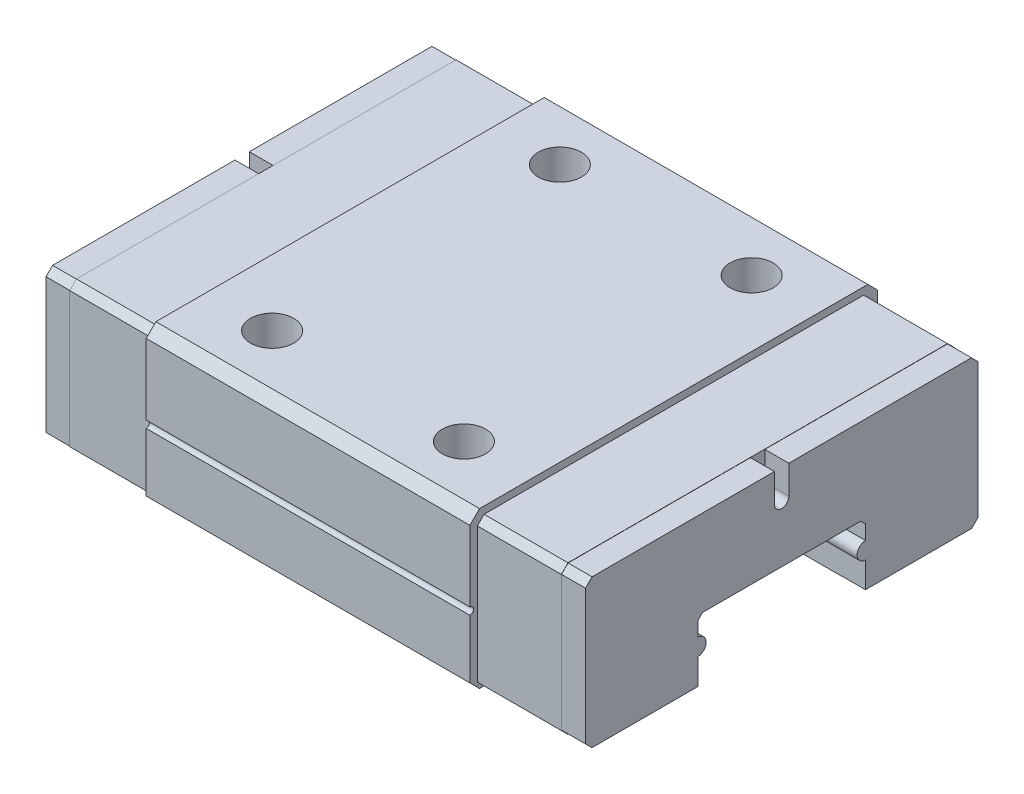
SolidWorks part; units mm, degrees
material "铸造合金钢"
ref_plane "前视基准面" through (0, 0, 0) normal (0, 0, 1) x (1, 0, 0)
ref_plane "上视基准面" through (0, 0, 0) normal (0, 1, 0) x (1, 0, 0)
ref_plane "右视基准面" through (0, 0, 0) normal (1, 0, 0) x (0, 0, -1)
sketch "草图1" plane through (0, 0, 0) normal (1, 0, 0) x (0, 0, -1)
  line L0 (0, 0) -> (0, 6.9969) construction
  line L1 (0, 0) -> (6.5228, 0) construction
  line L2 (-8.5, 2.8469) -> (-8.0969, 3.25)
  line L3 (-8.0969, 3.25) -> (8.0969, 3.25)
  line L4 (-8.5, 2.8469) -> (-8.5, -2.8469)
  line L5 (-8.0969, -3.25) -> (8.0969, -3.25)
  line L6 (8.5, 2.8469) -> (8.5, -2.8469)
  line L7 (-8.5, 3.25) -> (8.5, -3.25) construction
  line L8 (-8.5, -3.25) -> (8.5, 3.25) construction
  line L9 (8.0969, 3.25) -> (8.5, 2.8469)
  line L10 (8.0969, -3.25) -> (8.5, -2.8469)
  line L11 (-8.5, -2.8469) -> (-8.0969, -3.25)
  point P1 (0, 0)
  dimension "D1" = 6.5
  dimension "D2" = 17
  dimension "D3" = 0.57
  dimension "D5" = 0.57
  dimension "D9" = 0.57
  dimension "D10" = 225
  dimension "D7" = 0.57
  dimension "D4" = 225
  dimension "D6" = 225
  dimension "D8" = 225
extrude "凸台-拉伸1" add sketch "草图1" along normal blind 13.5
sketch "草图3" plane through (0, 0, 0) normal (-1, 0, 0) x (0, 0, 1)
  line L0 (0, 0) -> (0, 6.7455) construction
  line L1 (0, 0) -> (9.8711, 0) construction
  line L3 (8.5, 2.8469) -> (8.5, -2.8469) construction
  circle A0 centre (8.5, -0.2531) radius 0.15
  circle A1 centre (-8.5, -0.2531) radius 0.15
  dimension "D1" = 0.3
  dimension "D2" = 3.1
extrude "切除-拉伸2" cut sketch "草图3" against normal up to surface (13.5 mm away) up to face at (13.5, 0, 0)
sketch "草图4" plane through (0, 0, 0) normal (-1, 0, 0) x (0, 0, 1)
  line L0 (0, 0) -> (0, 6.8579) construction
  line L1 (0, 0) -> (4.1985, 0) construction
  line L3 (8.19, -2.9702) -> (8.19, 2.67)
  line L4 (-8.2, -2.9702) -> (-8.2, 2.67)
  line L5 (7.91, 2.95) -> (-7.92, 2.95)
  line L6 (8.0969, -3.25) -> (-8.0969, -3.25) construction
  line L7 (-8.2, 2.95) -> (8.2, -3.25) construction
  line L8 (8.19, 2.95) -> (-8.21, -3.25) construction
  line L9 (-8.0969, 3.25) -> (8.0969, 3.25) construction
  line L10 (-8.5, -2.8469) -> (-8.5, -0.4031) construction
  line L11 (-8.2, 2.67) -> (-7.92, 2.95)
  line L12 (-7.9302, -3.24) -> (-8.2, -2.9702)
  line L13 (7.9202, -3.24) -> (8.19, -2.9702)
  line L14 (8.19, 2.67) -> (7.91, 2.95)
  line L15 (-7.9302, -3.24) -> (7.9202, -3.24)
  point P12 (0, -0.15)
  dimension "D1" = 0.3
  dimension "D2" = 0.3
  dimension "D3" = 0.01
  dimension "D4" = 225
  dimension "D5" = 225
extrude "凸台-拉伸2" add sketch "草图4" along normal blind 3.5 and the other way blind 17
sketch "草图5" plane through (17, 0, 0) normal (1, 0, 0) x (0, 0, -1)
  line L9 (-7.9059, 2.94) -> (7.9159, 2.94)
  line L10 (7.9159, 2.94) -> (8.19, 2.6659)
  line L11 (8.19, 2.6659) -> (8.19, -2.966)
  line L12 (8.19, -2.966) -> (7.926, -3.23)
  line L13 (7.926, -3.23) -> (-7.9102, -3.23)
  line L14 (-7.9102, -3.23) -> (-8.18, -2.9602)
  line L15 (-8.18, -2.9602) -> (-8.18, 2.6659)
  line L16 (-8.18, 2.6659) -> (-7.9059, 2.94)
  line L17 (-8.19, 2.67) -> (-7.91, 2.95) construction
  line L18 (-7.9202, -3.24) -> (-8.19, -2.9702) construction
  line L20 (7.92, 2.95) -> (8.2, 2.67) construction
  line L21 (8.2, -2.9702) -> (7.9302, -3.24) construction
  line L22 (-7.91, 2.95) -> (7.92, 2.95) construction
  line L23 (7.9302, -3.24) -> (-7.9202, -3.24) construction
  line L24 (8.2, 2.67) -> (8.2, -2.9702) construction
  line L25 (-8.19, -2.9702) -> (-8.19, 2.67) construction
  dimension "D1" = 0.01
  dimension "D2" = 0.01
  dimension "D3" = 0.01
  dimension "D4" = 0.01
  dimension "D5" = 0.01
  dimension "D6" = 0.01
  dimension "D7" = 0.01
extrude "凸台-拉伸3" add sketch "草图5" along normal blind 1 and the other way blind 21.5
sketch "草图2" plane through (0, 3.25, 0) normal (0, 1, 0) x (1, 0, 0)
  line L0 (6.75, 0) -> (0, 0) construction
  line L1 (2.75, 6) -> (10.75, 6) construction
  line L2 (2.75, 6) -> (2.75, -6) construction
  line L3 (2.75, -6) -> (10.75, -6) construction
  line L4 (10.75, 6) -> (10.75, -6) construction
  line L5 (2.75, 6) -> (10.75, -6) construction
  line L6 (2.75, -6) -> (10.75, 6) construction
  line L8 (0, 8.0969) -> (0, -8.0969) construction
  circle A0 centre (2.75, 6) radius 0.9
  circle A1 centre (10.75, 6) radius 0.9
  circle A2 centre (10.75, -6) radius 0.9
  circle A3 centre (2.75, -6) radius 0.9
  point P0 (6.75, 0)
  dimension "D1" = 1.8
  dimension "D2" = 12
  dimension "D3" = 8
  dimension "D4" = 2.75
extrude "切除-拉伸1" cut sketch "草图2" against normal blind 2.5
sketch "草图6" plane through (18, 0, 0) normal (1, 0, 0) x (0, 0, -1)
  line L0 (0, 0) -> (0, 6.1749) construction
  line L1 (7.9159, 2.94) -> (-7.9059, 2.94) construction
  line L2 (0.3, 1.75) -> (0.3, 2.94)
  line L3 (-0.3, 1.75) -> (-0.3, 2.94)
  line L4 (-0.3, 2.94) -> (0.3, 2.94)
  circle A0 centre (0, 1.75) radius 0.3 construction
  arc A1 (-0.3, 1.75) -> (0.3, 1.75) centre (0, 1.75) ccw
  dimension "D1" = 0.6
  dimension "D2" = 1.19
extrude "切除-拉伸3" cut sketch "草图6" against normal blind 1
sketch "草图7" plane through (-4.5, 0, 0) normal (-1, 0, 0) x (0, 0, 1)
  line L0 (0, 0) -> (0, 4.4194) construction
  line L1 (-0.3, 1.75) -> (-0.3, 2.94)
  line L3 (0.3, 1.75) -> (0.3, 2.94)
  line L4 (-7.9159, 2.94) -> (7.9059, 2.94) construction
  line L5 (0.3, 2.94) -> (-0.3, 2.94)
  circle A0 centre (0, 1.75) radius 0.3 construction
  arc A1 (-0.3, 1.75) -> (0.3, 1.75) centre (0, 1.75) ccw
  dimension "D1" = 0.6
  dimension "D2" = 1.19
extrude "切除-拉伸4" cut sketch "草图7" against normal blind 1
sketch "草图8" plane through (-4.5, 0, 0) normal (-1, 0, 0) x (0, 0, 1)
  circle A0 centre (0, 1.75) radius 0.3
  arc A1 (-0.3, 1.75) -> (0.3, 1.75) centre (0, 1.75) ccw construction
extrude "切除-拉伸5" cut sketch "草图8" against normal up to surface (4.5 mm away) up to face at (0, -0.1475, -0.005)
sketch "草图9" plane through (18, 0, 0) normal (1, 0, 0) x (0, 0, -1)
  circle A0 centre (0, 1.75) radius 0.3
  arc A1 (-0.3, 1.75) -> (0.3, 1.75) centre (0, 1.75) ccw construction
extrude "切除-拉伸6" cut sketch "草图9" against normal up to surface (4.5 mm away) contours A0 up to face at (13.5, -0.1475, -0.005)
sketch "草图10" plane through (18, 0, 0) normal (1, 0, 0) x (0, 0, -1)
  line L0 (3.498, -2.15) -> (3.498, -3.25)
  line L1 (-8.0969, -3.25) -> (8.0969, -3.25) construction
  line L2 (0, -0.7312) -> (0, 0.7312) construction
  line L3 (0, 0) -> (2.7709, 0) construction
  line L4 (3.498, -1.45) -> (3.498, -0.85)
  line L5 (3.498, -0.85) -> (3.3, -0.652)
  line L6 (3.3, -0.652) -> (-3.3, -0.652)
  line L7 (-3.498, -2.15) -> (-3.498, -3.25)
  line L8 (-3.498, -1.45) -> (-3.498, -0.85)
  line L9 (-3.498, -0.85) -> (-3.3, -0.652)
  line L10 (-3.498, -3.25) -> (3.498, -3.25)
  circle A0 centre (3.498, -1.8) radius 0.35 construction
  arc A1 (3.498, -2.15) -> (3.498, -1.45) centre (3.498, -1.8) cw
  arc A2 (-3.498, -2.15) -> (-3.498, -1.45) centre (-3.498, -1.8) ccw
  point P8 (0, 0)
  point P25 (0, -0.652)
  dimension "D2" = 0.7
  dimension "D1" = 1.1
  dimension "D3" = 0.6
  dimension "D4" = 225
  dimension "D5" = 0.28
  dimension "D6" = 3.3
extrude "切除-拉伸7" cut sketch "草图10" against normal up to surface (22.5 mm away) up to face at (-4.5, 0.6588, -0.0038)
